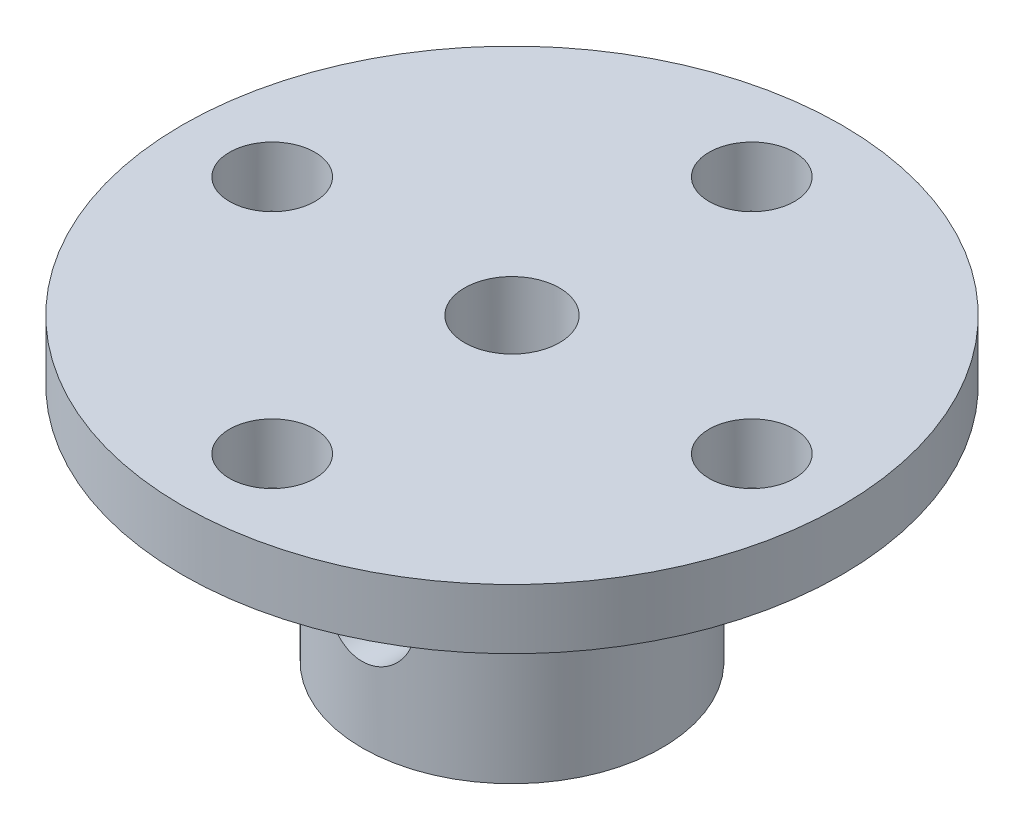
SolidWorks part; units mm, degrees
ref_plane "Front Plane" through (0, 0, 0) normal (0, 0, 1) x (1, 0, 0)
ref_plane "Top Plane" through (0, 0, 0) normal (0, 1, 0) x (1, 0, 0)
ref_plane "Right Plane" through (0, 0, 0) normal (1, 0, 0) x (0, 0, -1)
sketch "Sketch1" plane through (0, 0, 0) normal (0, 1, 0) x (1, 0, 0)
  circle A0 centre (0, 0) radius 11
  dimension "D1" = 22
extrude "Boss-Extrude1" add sketch "Sketch1" along normal blind 2
sketch "Sketch2" plane through (0, 0, 0) normal (0, 1, 0) x (1, 0, 0)
  circle A0 centre (0, 0) radius 5
  dimension "D1" = 10
extrude "Boss-Extrude2" add sketch "Sketch2" against normal blind 8
sketch "Sketch3" plane through (0, 2, 0) normal (0, -1, 0) x (-1, 0, 0)
  circle A0 centre (0, 0) radius 1.585
  dimension "D1" = 3.17
extrude "Cut-Extrude1" cut sketch "Sketch3" along normal through all
sketch "Sketch4" plane through (0, 2, 0) normal (0, 1, 0) x (1, 0, 0)
  circle A0 centre (0, 8) radius 1.425
  dimension "D1" = 2.85
  dimension "D2" = 8
extrude "Cut-Extrude2" cut sketch "Sketch4" against normal up to next (2 mm away)
pattern_circular "CirPattern1" count 4 over 360 about axis through (0, 0, 0) along (0, 1, 0) of "Cut-Extrude2"
sketch "Sketch5" plane through (0, 0, 0) normal (0, 0, 1) x (1, 0, 0)
  line L3 (-5, -4) -> (5, -4) construction
  line L4 (-5, 0) -> (-5, -8) construction
  line L5 (5, -8) -> (5, 0) construction
  line L6 (0, 0) -> (0, -8) construction
  line L7 (-5, -8) -> (5, -8) construction
  circle A0 centre (0, -4) radius 1.5
  dimension "D1" = 3
extrude "Cut-Extrude3" cut sketch "Sketch5" against normal through all both and the other way through all
